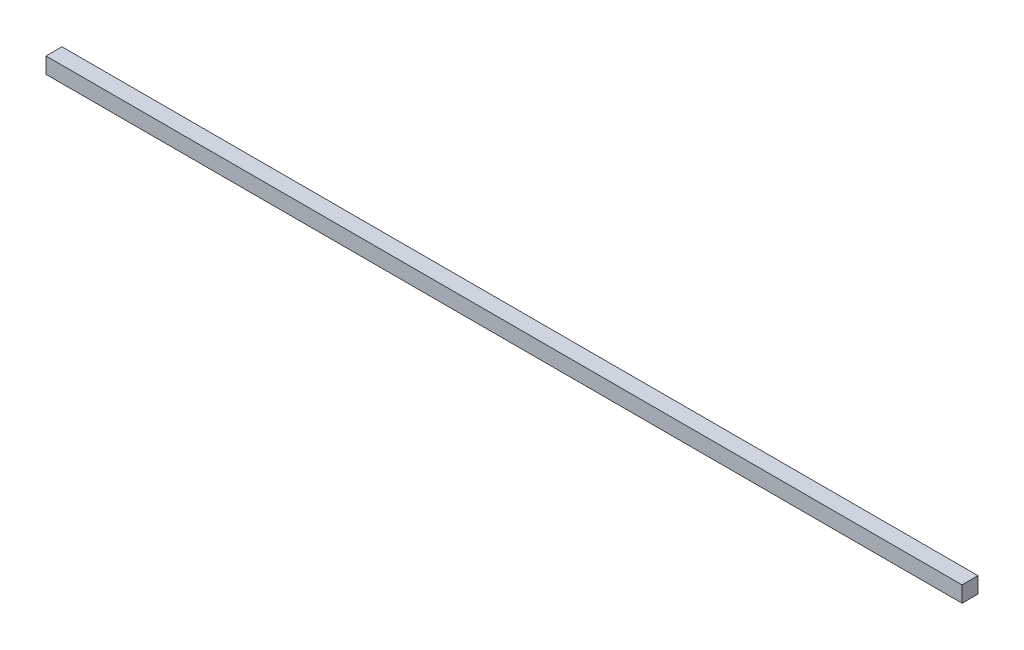
SolidWorks part; units mm, degrees
ref_plane "Спереди" through (0, 0, 0) normal (0, 0, 1) x (1, 0, 0)
ref_plane "Сверху" through (0, 0, 0) normal (0, 1, 0) x (1, 0, 0)
ref_plane "Справа" through (0, 0, 0) normal (1, 0, 0) x (0, 0, -1)
sketch "Эскиз1" plane through (0, 0, 0) normal (1, 0, 0) x (0, 0, -1)
  line L1 (0, 0) -> (20, 0)
  line L2 (0, 0) -> (0, 20)
  line L3 (0, 20) -> (20, 20)
  line L4 (20, 0) -> (20, 20)
extrude "Бобышка-Вытянуть1" add sketch "Эскиз1" along normal blind 1150
